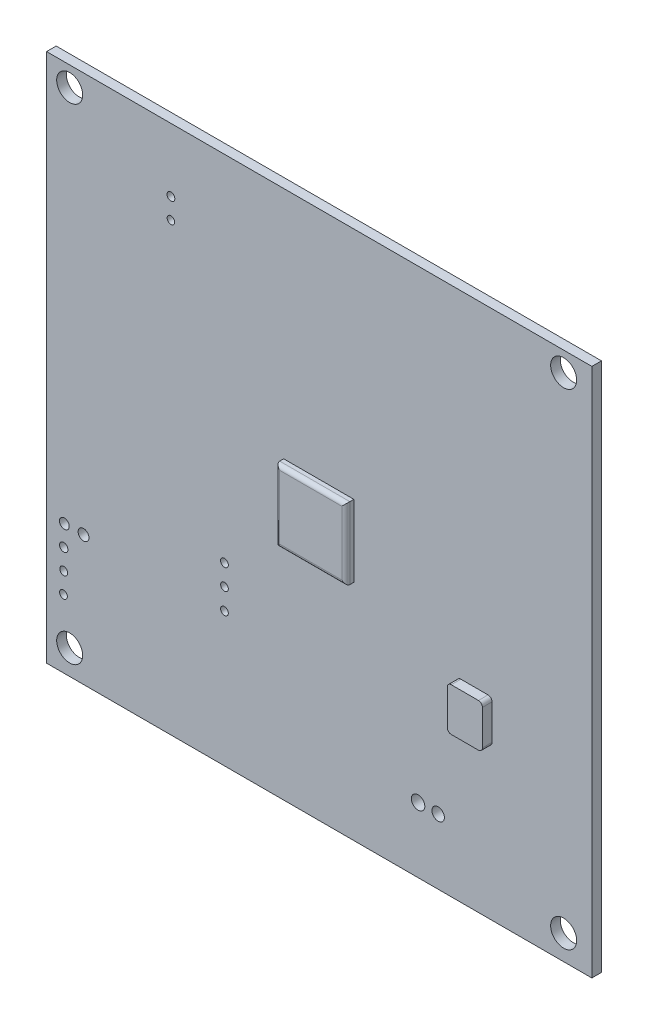
SolidWorks part; units mm, degrees
material "Plastique personnalisé"
ref_plane "Plan de face" through (0, 0, 0) normal (0, 0, 1) x (1, 0, 0)
ref_plane "Plan de dessus" through (0, 0, 0) normal (0, 1, 0) x (1, 0, 0)
ref_plane "Plan de droite" through (0, 0, 0) normal (1, 0, 0) x (0, 0, -1)
sketch "Esquisse1" plane through (0, 0, 0) normal (0, 0, 1) x (1, 0, 0)
  line L0 (18.3197, 280.5986) -> (86.4187, 280.2378) construction
  line L2 (18.3143, 279.9634) -> (86.4143, 279.9634)
  line L3 (18.3143, 279.9634) -> (18.3143, 213.8134)
  line L4 (18.3143, 213.8134) -> (86.4143, 213.8134)
  line L5 (86.4143, 279.9634) -> (86.4143, 213.8134)
  circle A0 centre (21.204, 216.9021) radius 1.625
  circle A1 centre (82.893, 216.9021) radius 1.625
  circle A2 centre (21.204, 277.5171) radius 1.625
  circle A3 centre (82.893, 277.5171) radius 1.625
  circle A4 centre (20.4609, 227.4248) radius 0.5199
  circle A5 centre (20.4609, 224.8579) radius 0.4966
  circle A6 centre (20.4289, 222.3041) radius 0.485
  circle A7 centre (20.5394, 230.0178) radius 0.609
  circle A8 centre (22.9379, 230.0178) radius 0.6779
  circle A9 centre (64.715, 221.9528) radius 0.8386
  circle A10 centre (67.2195, 221.9528) radius 0.7788
  circle A11 centre (40.5321, 235.7812) radius 0.4878
  circle A12 centre (40.5321, 233.1969) radius 0.4795
  circle A13 centre (40.5321, 230.5617) radius 0.4831
  circle A14 centre (33.847, 272.0506) radius 0.4895
  circle A15 centre (33.847, 269.5019) radius 0.4703
  dimension "D4" = 3.25
  dimension "D5" = 3.25
  dimension "D6" = 3.25
  dimension "D7" = 3.25
  dimension "D1" = 68.1
  dimension "D2" = 66.15
  dimension "D3" = 68.1
sketch "Esquisse2" plane through (0, 0, 0) normal (0, 0, 1) x (1, 0, 0)
  line L0 (18.3143, 279.9634) -> (18.3143, 213.8134) construction
  line L1 (18.3143, 256.4034) -> (29.2527, 256.4034)
  line L2 (18.3143, 256.4034) -> (18.3143, 240.3546)
  line L3 (18.3143, 240.3546) -> (29.2527, 240.3546)
  line L4 (29.2527, 256.4034) -> (29.2527, 240.3546)
  line L5 (43.335, 225.4524) -> (42.2507, 225.4524)
  line L6 (28.6639, 269.5999) -> (18.3143, 269.5999)
  line L7 (28.6639, 269.5999) -> (28.6639, 262.0476)
  line L8 (28.6639, 262.0476) -> (18.3143, 262.0476)
  line L9 (18.3143, 269.5999) -> (18.3143, 262.0476)
  line L10 (47.9294, 250.724) -> (56.6873, 250.724)
  line L11 (47.9294, 250.724) -> (47.9294, 241.748)
  line L12 (47.9294, 241.748) -> (56.6873, 241.748)
  line L13 (56.6873, 250.724) -> (56.6873, 241.748)
  line L14 (30.3825, 236.4808) -> (37.0834, 236.4808)
  line L15 (30.3825, 236.4808) -> (30.3825, 228.4709)
  line L16 (30.3825, 228.4709) -> (37.0834, 228.4709)
  line L17 (37.0834, 236.4808) -> (37.0834, 228.4709)
  line L18 (25.2191, 233.5316) -> (28.3381, 233.5316)
  line L19 (25.2191, 233.5316) -> (25.2191, 227.2936)
  line L20 (25.2191, 227.2936) -> (28.3381, 227.2936)
  line L21 (28.3381, 233.5316) -> (28.3381, 227.2936)
  line L22 (47.4017, 274.1173) -> (50.8559, 274.1173)
  line L23 (47.4017, 274.1173) -> (47.4017, 266.9868)
  line L24 (47.4017, 266.9868) -> (50.8559, 266.9868)
  line L25 (50.8559, 274.1173) -> (50.8559, 266.9868)
  line L26 (69.0979, 238.425) -> (74.4931, 238.425)
  line L27 (69.0979, 238.425) -> (69.0979, 231.9893)
  line L28 (69.0979, 231.9893) -> (74.4931, 231.9893)
  line L29 (74.4931, 238.425) -> (74.4931, 231.9893)
  line L30 (42.2507, 225.4524) -> (42.2507, 219.7447)
  line L31 (42.2507, 219.7447) -> (61.1206, 219.7447)
  line L32 (61.1206, 219.7447) -> (61.2411, 225.4524)
  line L33 (61.2411, 225.4524) -> (60.3074, 225.4524)
  line L34 (60.3074, 225.4524) -> (59.4038, 226.7023)
  line L35 (59.4038, 226.7023) -> (44.5398, 226.7023)
  line L36 (44.5398, 226.7023) -> (43.4555, 225.4524)
  line L37 (43.335, 225.4524) -> (43.4555, 225.4524)
extrude "Boss.-Extru.1" add sketch "Esquisse1" against normal blind 1.2
sketch "Esquisse3" plane through (0, 0, 0) normal (0, 0, 1) x (1, 0, 0)
  line L1 (47.9294, 250.724) -> (56.6873, 250.724)
  line L2 (47.9294, 250.724) -> (47.9294, 241.748)
  line L3 (47.9294, 241.748) -> (56.6873, 241.748)
  line L4 (56.6873, 250.724) -> (56.6873, 241.748)
extrude "Boss.-Extru.2" add sketch "Esquisse3" along normal blind 1
fillet "Congé1" radius 0.5 4 edges at (47.9294, 246.236, 1) (52.3084, 250.724, 1) (56.6873, 246.236, 1) (52.3084, 241.748, 1)
sketch "Esquisse4" plane through (0, 0, 0) normal (0, 0, 1) x (1, 0, 0)
  line L1 (69.5573, 237.9513) -> (73.9529, 237.9513)
  line L2 (69.5573, 237.9513) -> (69.5573, 232.5726)
  line L3 (69.5573, 232.5726) -> (73.9529, 232.5726)
  line L4 (73.9529, 237.9513) -> (73.9529, 232.5726)
extrude "Boss.-Extru.3" add sketch "Esquisse4" along normal blind 1.2
fillet "Congé2" radius 0.5 4 edges at (73.9529, 237.9513, 0.6) (69.5573, 237.9513, 0.6) (69.5573, 232.5726, 0.6) (73.9529, 232.5726, 0.6)
